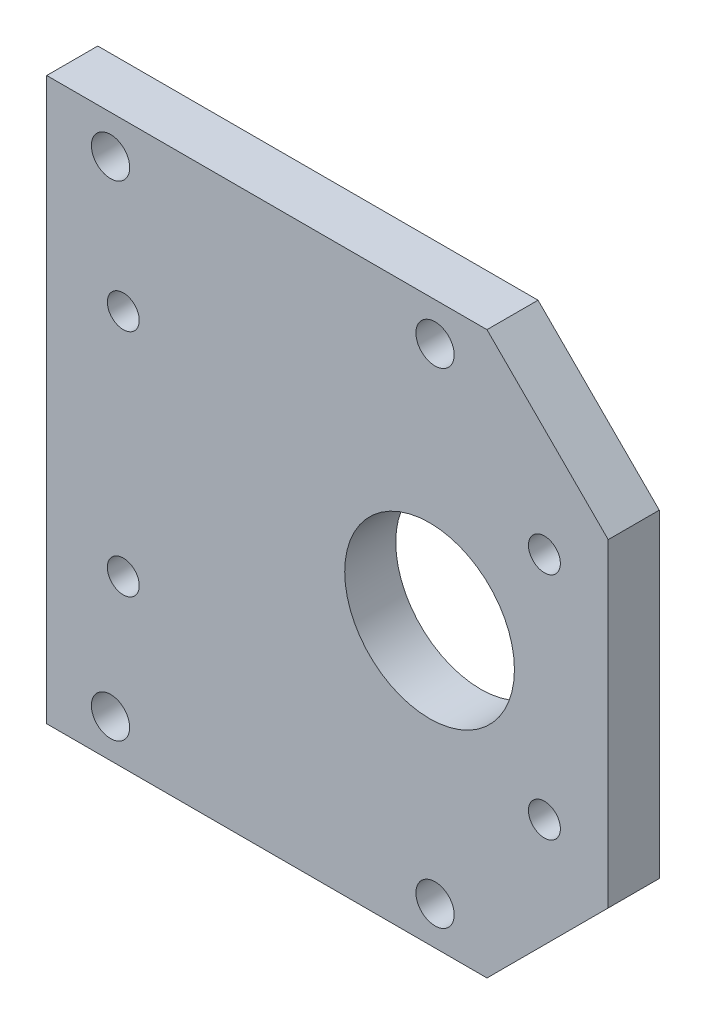
SolidWorks part; units mm, degrees
ref_plane "Front Plane" through (0, 0, 0) normal (0, 0, 1) x (1, 0, 0)
ref_plane "Top Plane" through (0, 0, 0) normal (0, 1, 0) x (1, 0, 0)
ref_plane "Right Plane" through (0, 0, 0) normal (1, 0, 0) x (0, 0, -1)
sketch "Sketch1" plane through (0, 0, 0) normal (0, 0, 1) x (1, 0, 0)
  line L0 (22, 12.5) -> (22, -12.5)
  line L1 (22, -12.5) -> (12.5, -22)
  line L2 (12.5, -22) -> (-22, -22)
  line L3 (-22, -22) -> (-22, 22)
  line L4 (-22, 22) -> (12.5, 22)
  line L5 (12.5, 22) -> (22, 12.5)
  line L6 (23, -14.5) -> (23, 14.5) construction
  line L7 (0, 0) -> (22, 0) construction
  line L8 (21.5, 16) -> (-21.5, 16) construction
  line L9 (-21.5, -16) -> (21.5, -16) construction
  line L10 (-23, 14.5) -> (-23, -14.5) construction
  circle A0 centre (8, 0) radius 6.65 construction
  circle A1 centre (8, 0) radius 6.65
  circle A2 centre (17, 9) radius 1.25 construction
  circle A3 centre (17, -9) radius 1.25 construction
  circle A4 centre (17, 9) radius 1.25
  circle A5 centre (17, -9) radius 1.25
  circle A6 centre (-16, 9) radius 1.25 construction
  circle A7 centre (-16, -9) radius 1.25 construction
  circle A8 centre (-16, 9) radius 1.25
  circle A9 centre (-16, -9) radius 1.25
  dimension "D1" = 1
  dimension "D2" = 135
  dimension "D3" = 135
  dimension "D4" = 25
  dimension "D5" = 6
  dimension "D6" = 6
  dimension "D7" = 1
extrude "Boss-Extrude1" add sketch "Sketch1" along normal blind 4
sketch "Sketch2" plane through (0, 0, 4) normal (0, 0, 1) x (1, 0, 0)
  line L0 (-22, -19) -> (23.3054, -19) construction
  line L1 (-22, 22) -> (-22, -22) construction
  line L2 (-22, -22) -> (12.5, -22) construction
  line L3 (22, 0) -> (-22, 0) construction
  line L4 (22, -12.5) -> (22, 12.5) construction
  line L5 (12.5, -22) -> (22, -12.5) construction
  circle A0 centre (-17, -19) radius 1.5
  circle A1 centre (8.4289, -19) radius 1.5
  circle A2 centre (-17, 19) radius 1.5
  circle A3 centre (8.4289, 19) radius 1.5
  dimension "D2" = 3
  dimension "D1" = 3
  dimension "D3" = 5
  dimension "D4" = 5
extrude "Cut-Extrude1" cut sketch "Sketch2" against normal through all
